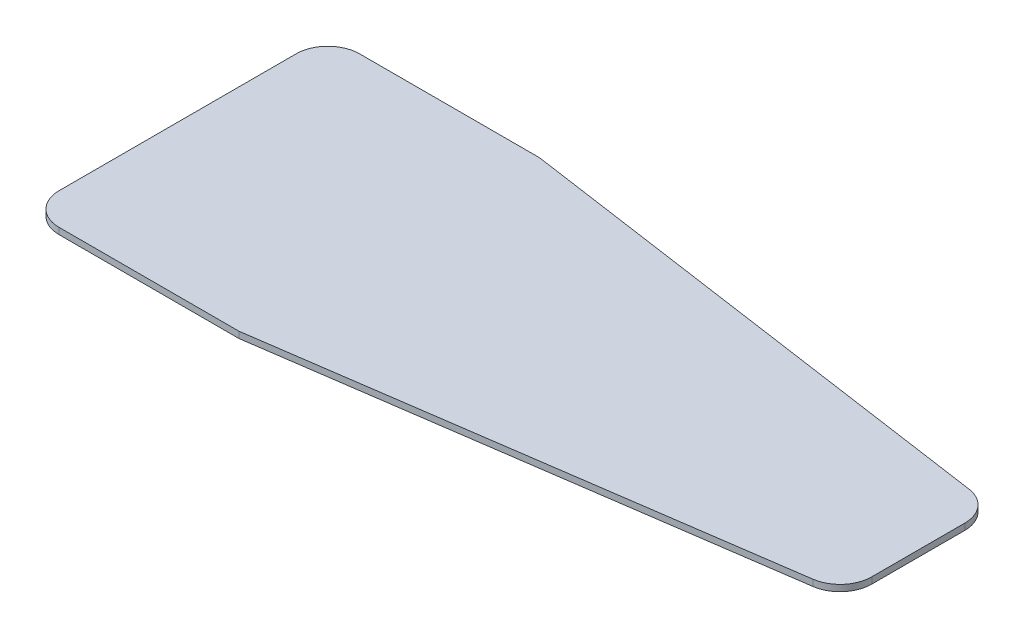
SolidWorks part; units mm, degrees
ref_plane "Front Plane" through (0, 0, 0) normal (0, 0, 1) x (1, 0, 0)
ref_plane "Top Plane" through (0, 0, 0) normal (0, 1, 0) x (1, 0, 0)
ref_plane "Right Plane" through (0, 0, 0) normal (1, 0, 0) x (0, 0, -1)
sketch "Sketch1" plane through (0, 0, 0) normal (0, 1, 0) x (1, 0, 0)
  line L0 (-21.9346, 71) -> (377.6567, 71) construction
  line L1 (15, 0) -> (100, 0)
  line L2 (0, 15) -> (0, 127)
  line L3 (15, 142) -> (100, 142)
  line L4 (350, 48.9947) -> (350, 93.0053)
  line L5 (100, 142) -> (337.1379, 107.8521)
  line L6 (337.1379, 34.1479) -> (100, 0)
  arc A0 (337.1379, 34.1479) -> (350, 48.9947) centre (335, 48.9947) ccw
  arc A1 (337.1379, 107.8521) -> (350, 93.0053) centre (335, 93.0053) cw
  arc A2 (15, 0) -> (0, 15) centre (15, 15) cw
  arc A3 (0, 127) -> (15, 142) centre (15, 127) cw
  point P9 (0, 71)
  point P12 (350, 36)
  point P15 (350, 106)
  point P18 (0, 0)
  point P21 (0, 142)
  dimension "D1" = 15
  dimension "D2" = 142
  dimension "D3" = 100
  dimension "D4" = 35
  dimension "D5" = 35
extrude "Boss-Extrude1" add sketch "Sketch1" along normal blind 3
